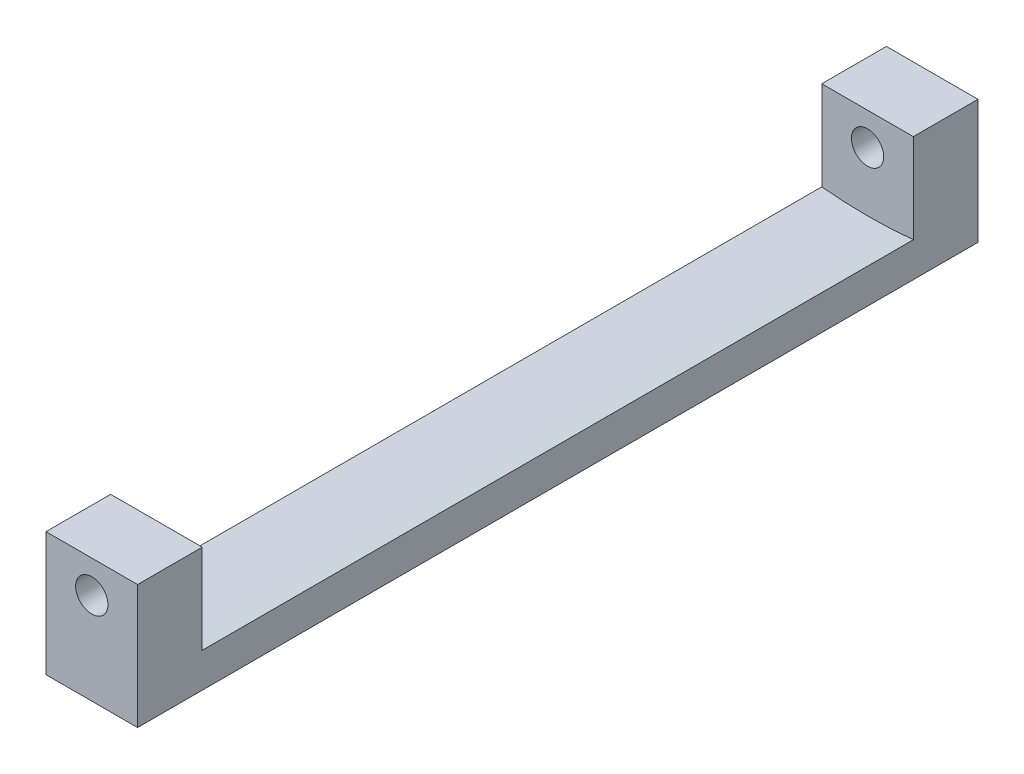
SolidWorks part; units mm, degrees
ref_plane "Front Plane" through (0, 0, 0) normal (0, 0, 1) x (1, 0, 0)
ref_plane "Top Plane" through (0, 0, 0) normal (0, 1, 0) x (1, 0, 0)
ref_plane "Right Plane" through (0, 0, 0) normal (1, 0, 0) x (0, 0, -1)
sketch "Sketch1" plane through (0, 0, 0) normal (0, 0, 1) x (1, 0, 0)
  line L0 (0, 0) -> (0, -49.2842) construction
  line L1 (-4.25, -45.5) -> (4.25, -45.5)
  line L2 (-4.25, -45.5) -> (-4.25, -42.287)
  line L3 (4.25, -45.5) -> (4.25, -42.287)
  arc A0 (-4.25, -42.287) -> (4.25, -42.287) centre (0, 0) ccw
  arc A1 (-4.25, -42.287) -> (4.25, -42.287) centre (0, 0) ccw
  point P4 (0, -45.5)
  point P5 (0, -42.5)
  point P9 (0, -45.5)
  dimension "D1" = 85
  dimension "D2" = 3
  dimension "D3" = 8.5
extrude "Boss-Extrude1" add sketch "Sketch1" along normal blind 78 contours L0 A0 L2 L1 | A1 L0 L1 L3
ref_plane "Plane1" through (0, -42.5, 0) normal (0, -1, 0) x (-1, 0, 0)
sketch "Sketch2" plane through (0, -42.5, 0) normal (0, -1, 0) x (-1, 0, 0)
  line L0 (4.25, -78) -> (4.25, 0) construction
  line L1 (-4.25, -78) -> (4.25, -78)
  line L2 (-4.25, -78) -> (-4.25, -72)
  line L3 (-4.25, -72) -> (4.25, -72)
  line L4 (4.25, -78) -> (4.25, -72)
  line L5 (-4.25, -78) -> (-4.25, 0) construction
  line L6 (4.25, 0) -> (-4.25, 0)
  line L7 (4.25, 0) -> (4.25, -6)
  line L8 (4.25, -6) -> (-4.25, -6)
  line L9 (-4.25, 0) -> (-4.25, -6)
  dimension "D1" = 6
  dimension "D2" = 6
extrude "Boss-Extrude2" add sketch "Sketch2" against normal blind 8.5
sketch "Sketch3" plane through (0, 0, 0) normal (0, 0, -1) x (-1, 0, 0)
  line L0 (4.25, -45.5) -> (4.25, -34) construction
  line L1 (4.25, -34) -> (-4.25, -34) construction
  circle A0 centre (0, -37) radius 1.5
  dimension "D1" = 3
  dimension "D2" = 4.25
  dimension "D3" = 3
extrude "Cut-Extrude1" cut sketch "Sketch3" against normal blind 100
